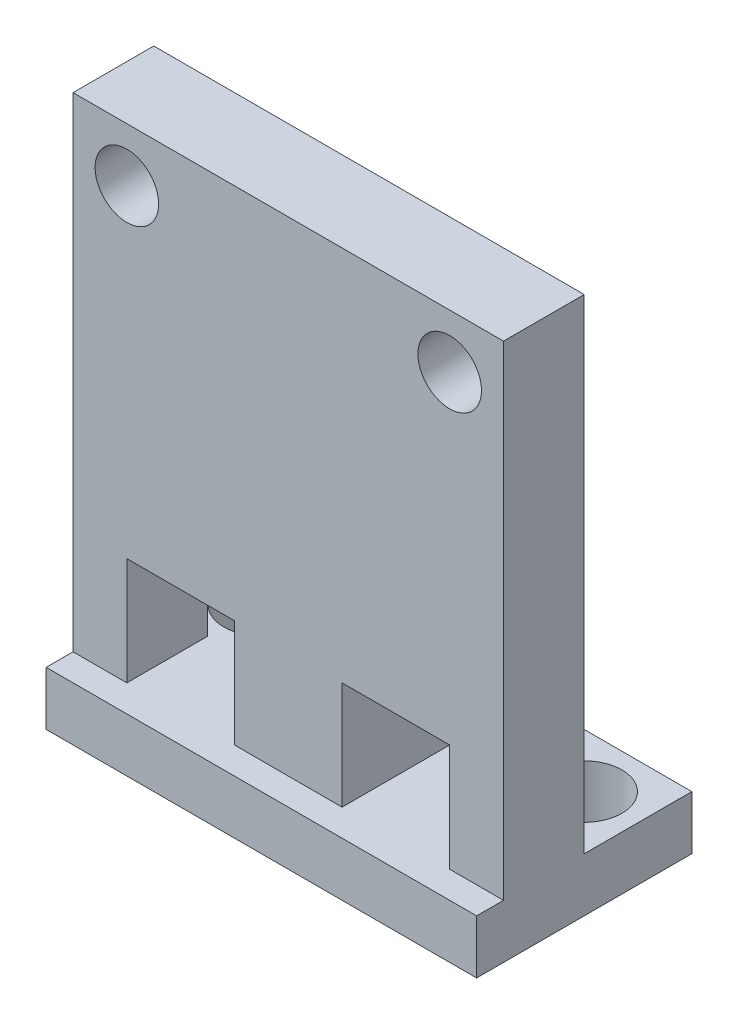
SolidWorks part; units mm, degrees
ref_plane "Front Plane" through (0, 0, 0) normal (0, 0, 1) x (1, 0, 0)
ref_plane "Top Plane" through (0, 0, 0) normal (0, 1, 0) x (1, 0, 0)
ref_plane "Right Plane" through (0, 0, 0) normal (1, 0, 0) x (0, 0, -1)
sketch "Sketch1" plane through (0, 0, 0) normal (0, 0, 1) x (1, 0, 0)
  line L1 (0, 0) -> (20.32, 0)
  line L2 (0, 0) -> (0, 25.4)
  line L3 (0, 25.4) -> (20.32, 25.4)
  line L4 (20.32, 0) -> (20.32, 25.4)
  dimension "D1" = 20.32
  dimension "D2" = 25.4
extrude "Boss-Extrude1" add sketch "Sketch1" along normal blind 5.08
sketch "Sketch2" plane through (0, 0, 5.08) normal (0, 0, 1) x (1, 0, 0)
  line L1 (0, 25.4) -> (0, 0) construction
  line L2 (20.32, 25.4) -> (0, 25.4) construction
  circle A0 centre (2.54, 22.86) radius 1.5
  circle A1 centre (17.78, 22.86) radius 1.5
  dimension "D4" = 3
  dimension "D1" = 15.24
  dimension "D2" = 2.54
  dimension "D3" = 2.54
extrude "Electronics Holes" cut sketch "Sketch2" against normal up to next
sketch "Sketch3" plane through (0, 0, 0) normal (0, -1, 0) x (1, 0, 0)
  line L0 (20.32, 5.08) -> (20.32, 0) construction
  line L1 (0, 5.08) -> (20.32, 5.08)
  line L2 (0, 5.08) -> (0, -5.08)
  line L3 (0, -5.08) -> (20.32, -5.08)
  line L4 (20.32, 5.08) -> (20.32, -5.08)
  dimension "D1" = 10.16
extrude "Boss-Extrude2" add sketch "Sketch3" against normal blind 2.54
sketch "Sketch4" plane through (0, 0, 5.08) normal (0, 0, 1) x (1, 0, 0)
  line L0 (0, 25.4) -> (0, 0) construction
  line L1 (20.32, 25.4) -> (0, 25.4)
  line L2 (20.32, 25.4) -> (20.32, 2.54)
  line L3 (20.32, 2.54) -> (0, 2.54)
  line L4 (0, 25.4) -> (0, 2.54)
  line L5 (0, 0) -> (20.32, 0) construction
  dimension "D1" = 2.54
extrude "Cut-Extrude2" cut sketch "Sketch4" against normal blind 1.27
sketch "Sketch5" plane through (0, 2.54, 0) normal (0, 1, 0) x (1, 0, 0)
  line L0 (20.32, 5.08) -> (20.32, 0) construction
  line L1 (0, 0) -> (0, 5.08) construction
  line L2 (20.32, 0) -> (0, 0) construction
  circle A0 centre (17.78, 2.54) radius 1.778
  circle A1 centre (2.54, 2.54) radius 1.778
  dimension "D1" = 3.556
  dimension "D2" = 2.54
  dimension "D3" = 2.54
  dimension "D4" = 2.54
extrude "Placement Holes" cut sketch "Sketch5" against normal blind 2.54
sketch "Sketch6" plane through (0, 0, 3.81) normal (0, 0, 1) x (1, 0, 0)
  line L0 (0, 2.54) -> (20.32, 2.54) construction
  line L1 (2.54, 2.54) -> (17.78, 2.54)
  line L2 (2.54, 2.54) -> (2.54, 7.62)
  line L3 (2.54, 7.62) -> (17.78, 7.62)
  line L4 (17.78, 2.54) -> (17.78, 7.62)
  line L5 (0, 25.4) -> (0, 2.54) construction
  dimension "D1" = 15.24
  dimension "D2" = 5.08
  dimension "D3" = 2.54
extrude "Cut-Extrude4" cut sketch "Sketch6" against normal through all
ref_plane "Plane1" through (10.16, 0, 0) normal (-1, 0, 0) x (0, 0, 1)
sketch "Sketch7" plane through (10.16, 0, 0) normal (-1, 0, 0) x (0, 0, 1)
  line L0 (0, 25.4) -> (-5.08, 2.54)
  line L3 (-5.08, 2.54) -> (3.81, 2.54)
  line L4 (3.81, 2.54) -> (3.81, 25.4)
  line L5 (3.81, 25.4) -> (0, 25.4)
extrude "Boss-Extrude3" add sketch "Sketch7" along normal blind 2.54
mirror "Mirror1" about plane through (10.16, 0, 0) normal (-1, 0, 0) of "Boss-Extrude3"
